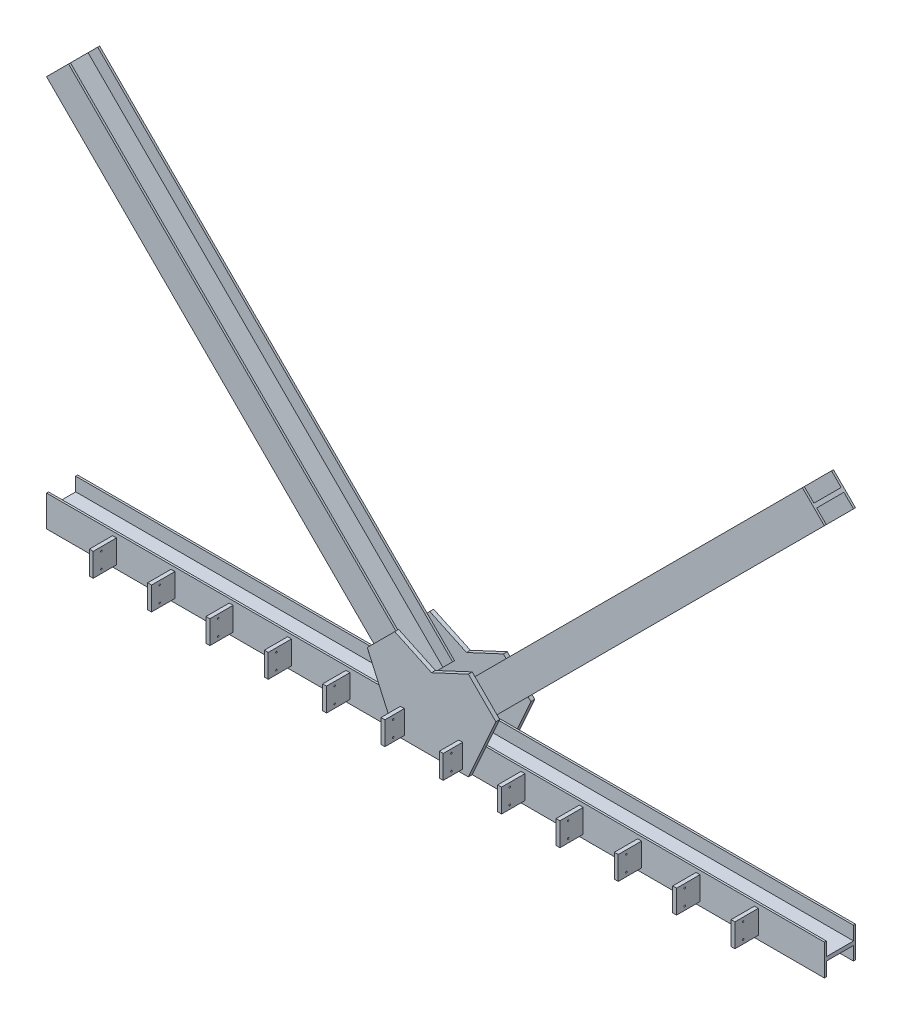
SolidWorks part; units mm, degrees
ref_plane "Front Plane" through (0, 0, 0) normal (0, 0, 1) x (1, 0, 0)
ref_plane "Top Plane" through (0, 0, 0) normal (0, 1, 0) x (1, 0, 0)
ref_plane "Right Plane" through (0, 0, 0) normal (1, 0, 0) x (0, 0, -1)
sketch "Sketch1" plane through (0, 0, 0) normal (0, 0, 1) x (1, 0, 0)
  line L0 (0, 0) -> (0, 2858.3993) construction
  line L2 (5000, -200) -> (-5000, -200)
  line L3 (5000, -200) -> (5000, 200)
  line L4 (5000, 200) -> (-5000, 200)
  line L5 (-5000, -200) -> (-5000, 200)
  line L6 (5000, -200) -> (-5000, 200) construction
  line L7 (5000, 200) -> (-5000, -200) construction
  dimension "D1" = 10000
  dimension "D2" = 400
extrude "Boss-Extrude1" add sketch "Sketch1" along normal blind 400
sketch "Sketch2" plane through (0, 0, 400) normal (0, 0, 1) x (1, 0, 0)
  line L0 (0, 200) -> (0, 1181.6652) construction
  line L1 (5000, 200) -> (-5000, 200) construction
  line L2 (-826.5659, 590.9345) -> (-473.0125, 944.4879)
  line L3 (-473.0125, 944.4879) -> (0, 723.9185)
  line L4 (-826.5659, 590.9345) -> (-473.0125, -200)
  line L5 (-5000, -200) -> (5000, -200) construction
  line L6 (-473.0125, -200) -> (0, -200)
  line L7 (826.5659, 590.9345) -> (473.0125, -200)
  line L8 (826.5659, 590.9345) -> (473.0125, 944.4879)
  line L9 (473.0125, 944.4879) -> (0, 723.9185)
  line L10 (473.0125, -200) -> (0, -200)
  point P15 (0, 723.9185)
  point P16 (-473.0125, -200)
  dimension "D1" = 45
  dimension "D2" = 110
  dimension "D3" = 500
extrude "Boss-Extrude2" add sketch "Sketch2" along normal blind 50
sketch "Sketch3" plane through (0, 0, 0) normal (0, 0, -1) x (-1, 0, 0)
  line L0 (-826.5659, 590.9345) -> (-473.0125, -200)
  line L2 (473.0125, -200) -> (-473.0125, -200)
  line L3 (5000, -200) -> (-5000, -200) construction
  line L4 (826.5659, 590.9345) -> (651.8154, 200) construction
  line L7 (-826.5659, 590.9345) -> (-651.8154, 200)
  line L8 (-651.8154, 200) -> (651.8154, 200)
  line L9 (651.8154, 200) -> (826.5659, 590.9345)
  line L10 (826.5659, 590.9345) -> (473.0125, 944.4879)
  line L11 (473.0125, 944.4879) -> (0, 723.9185)
  line L12 (0, 723.9185) -> (-473.0125, 944.4879)
  line L13 (-473.0125, 944.4879) -> (-826.5659, 590.9345)
  line L17 (826.5659, 590.9345) -> (473.0125, 944.4879)
  line L18 (473.0125, 944.4879) -> (0, 723.9185)
  line L19 (0, 723.9185) -> (-473.0125, 944.4879)
  line L20 (-473.0125, 944.4879) -> (-826.5659, 590.9345)
  line L21 (826.5659, 590.9345) -> (473.0125, -200)
  dimension "D1" = 0
extrude "Boss-Extrude3" add sketch "Sketch3" along normal blind 50
sketch "Sketch4" plane through (0, 0, 0) normal (0, 0, 1) x (1, 0, 0)
  line L0 (-437.6572, 272.7364) -> (-154.8145, 555.5792)
  line L1 (-154.8145, 555.5792) -> (-4717.1573, 5117.922)
  line L2 (-4717.1573, 5117.922) -> (-5000, 4835.0793)
  line L3 (-5000, 4835.0793) -> (-437.6572, 272.7364)
  line L4 (-473.0125, 944.4879) -> (-826.5659, 590.9345) construction
  line L5 (0, 0) -> (0, 2224.399) construction
  line L6 (154.8145, 555.5792) -> (4717.1573, 5117.922)
  line L7 (437.6572, 272.7364) -> (154.8145, 555.5792)
  line L8 (5000, 4835.0793) -> (437.6572, 272.7364)
  line L9 (4717.1573, 5117.922) -> (5000, 4835.0793)
  line L10 (-5000, 4835.0793) -> (-5000, 200) construction
  dimension "D1" = 90
  dimension "D2" = 90
  dimension "D3" = 400
  dimension "D4" = 50
  dimension "D5" = 500
extrude "Boss-Extrude4" add sketch "Sketch4" along normal blind 400
sketch "Sketch6" plane through (0, 0, 400) normal (0, 0, 1) x (1, 0, 0)
  line L0 (-5000, 0) -> (0, 0) construction
  line L1 (-5000, 200) -> (-5000, -200) construction
  line L2 (-3350, -150) -> (-3350, 150)
  line L3 (-4150, -150) -> (-4100, -150)
  line L4 (-4150, -150) -> (-4150, 150)
  line L5 (-4150, 150) -> (-4100, 150)
  line L6 (-4100, -150) -> (-4100, 150)
  line L7 (-4150, -150) -> (-4100, 150) construction
  line L8 (-4150, 150) -> (-4100, -150) construction
  line L9 (-3400, 150) -> (-3350, 150)
  line L10 (-3400, -150) -> (-3350, -150)
  line L11 (-2600, -150) -> (-2600, 150)
  line L12 (-2650, 150) -> (-2600, 150)
  line L13 (-2650, -150) -> (-2600, -150)
  line L14 (-1850, -150) -> (-1850, 150)
  line L15 (-1900, 150) -> (-1850, 150)
  line L16 (-1900, -150) -> (-1850, -150)
  line L17 (-1100, -150) -> (-1100, 150)
  line L18 (-1150, 150) -> (-1100, 150)
  line L19 (-1150, -150) -> (-1100, -150)
  line L20 (-350, -150) -> (-350, 150)
  line L21 (-400, 150) -> (-350, 150)
  line L22 (-400, -150) -> (-350, -150)
  line L23 (400, -150) -> (400, 150)
  line L24 (350, 150) -> (400, 150)
  line L25 (350, -150) -> (400, -150)
  line L26 (1150, -150) -> (1150, 150)
  line L27 (1100, 150) -> (1150, 150)
  line L28 (1100, -150) -> (1150, -150)
  line L29 (1900, -150) -> (1900, 150)
  line L30 (1850, 150) -> (1900, 150)
  line L31 (1850, -150) -> (1900, -150)
  line L32 (2650, -150) -> (2650, 150)
  line L33 (2600, 150) -> (2650, 150)
  line L34 (2600, -150) -> (2650, -150)
  line L35 (3400, -150) -> (3400, 150)
  line L36 (3350, 150) -> (3400, 150)
  line L37 (3350, -150) -> (3400, -150)
  line L38 (4150, -150) -> (4150, 150)
  line L39 (4100, 150) -> (4150, 150)
  line L40 (4100, -150) -> (4150, -150)
  line L41 (-3400, -150) -> (-3400, 150)
  line L42 (-2650, -150) -> (-2650, 150)
  line L43 (-1900, -150) -> (-1900, 150)
  line L44 (-1150, -150) -> (-1150, 150)
  line L45 (-400, -150) -> (-400, 150)
  line L46 (350, -150) -> (350, 150)
  line L47 (1100, -150) -> (1100, 150)
  line L48 (1850, -150) -> (1850, 150)
  line L49 (2600, -150) -> (2600, 150)
  line L50 (3350, -150) -> (3350, 150)
  line L51 (4100, -150) -> (4100, 150)
  point P6 (-4125, 0)
  dimension "D1" = 50
  dimension "D2" = 300
  dimension "D4" = 12
  dimension "D5" = 700
  dimension "D6" = 350
  dimension "D3" = 12
extrude "Boss-Extrude6" add sketch "Sketch6" along normal blind 300
sketch "Sketch7" plane through (-4917.5396, 4917.5396, 0) normal (-0.7071, 0.7071, 0) x (0, 0, 1)
  line L0 (25, 283.3834) -> (25, 108.3834)
  line L8 (400, 283.3834) -> (0, 283.3834) construction
  line L22 (25, 108.3834) -> (375, 108.3834)
  line L23 (375, 108.3834) -> (375, 283.3834)
  line L24 (375, 283.3834) -> (25, 283.3834)
  line L25 (200, 283.3834) -> (200, -116.6166) construction
  line L26 (400, -116.6166) -> (0, -116.6166) construction
  line L27 (400, 83.3834) -> (0, 83.3834) construction
  line L28 (400, 283.3834) -> (400, -116.6166) construction
  line L29 (0, -116.6166) -> (0, 283.3834) construction
  line L30 (0, 283.3834) -> (0, -116.6166) construction
  line L31 (375, -116.6166) -> (25, -116.6166)
  line L32 (375, 58.3834) -> (375, -116.6166)
  line L33 (25, 58.3834) -> (375, 58.3834)
  line L34 (25, -116.6166) -> (25, 58.3834)
  dimension "D1" = 25
  dimension "D2" = 25
extrude "Cut-Extrude1" cut sketch "Sketch7" against normal blind 6462
sketch "Sketch8" plane through (4917.5396, 4917.5396, 0) normal (0.7071, 0.7071, 0) x (0, 0, -1)
  line L0 (-200, 283.3834) -> (-200, -116.6166) construction
  line L1 (-400, 283.3834) -> (0, 283.3834) construction
  line L2 (-400, -116.6166) -> (0, -116.6166) construction
  line L3 (0, 83.3834) -> (-400, 83.3834) construction
  line L4 (0, -116.6166) -> (0, 283.3834) construction
  line L5 (-400, -116.6166) -> (-400, 283.3834) construction
  line L6 (-400, -116.6166) -> (-400, 283.3834) construction
  line L7 (-375, 283.3834) -> (-25, 283.3834)
  line L8 (-375, 283.3834) -> (-375, 108.3834)
  line L9 (-375, 108.3834) -> (-25, 108.3834)
  line L10 (-25, 283.3834) -> (-25, 108.3834)
  line L11 (-25, -116.6166) -> (-25, 58.3834)
  line L12 (-375, 58.3834) -> (-25, 58.3834)
  line L13 (-375, -116.6166) -> (-375, 58.3834)
  line L14 (-375, -116.6166) -> (-25, -116.6166)
  dimension "D1" = 25
  dimension "D2" = 25
  dimension "D3" = 25
extrude "Cut-Extrude2" cut sketch "Sketch8" against normal blind 6475
sketch "Sketch9" plane through (5000, 0, 0) normal (1, 0, 0) x (0, 0, -1)
  line L0 (-200, 200) -> (-200, -200) construction
  line L1 (-400, 200) -> (0, 200) construction
  line L2 (-400, -200) -> (0, -200) construction
  line L3 (0, 0) -> (-400, 0) construction
  line L4 (-400, -200) -> (-400, 200) construction
  line L5 (-400, -150) -> (-400, 150) construction
  line L6 (-375, 200) -> (-25, 200)
  line L7 (-375, 200) -> (-375, 25)
  line L8 (-375, 25) -> (-25, 25)
  line L9 (-25, 200) -> (-25, 25)
  line L10 (0, -200) -> (0, 200) construction
  line L11 (-25, -200) -> (-25, -25)
  line L12 (-375, -25) -> (-25, -25)
  line L13 (-375, -200) -> (-375, -25)
  line L14 (-375, -200) -> (-25, -200)
  dimension "D1" = 25
  dimension "D2" = 25
  dimension "D3" = 25
extrude "Cut-Extrude3" cut sketch "Sketch9" against normal blind 10052
sketch "Sketch10" plane through (4150, 0, 0) normal (1, 0, 0) x (0, 0, -1)
  line L0 (-594.8912, 150) -> (-594.8912, -150) construction
  line L1 (-700, 150) -> (-400, 150) construction
  line L2 (-700, -150) -> (-400, -150) construction
  line L3 (-594.8912, 0) -> (-700, 0) construction
  line L4 (-700, -150) -> (-700, 150) construction
  circle A0 centre (-594.8912, 100) radius 10
  circle A1 centre (-594.8912, -100) radius 10
  dimension "D1" = 20
  dimension "D2" = 50
extrude "Cut-Extrude4" cut sketch "Sketch10" against normal blind 8436
